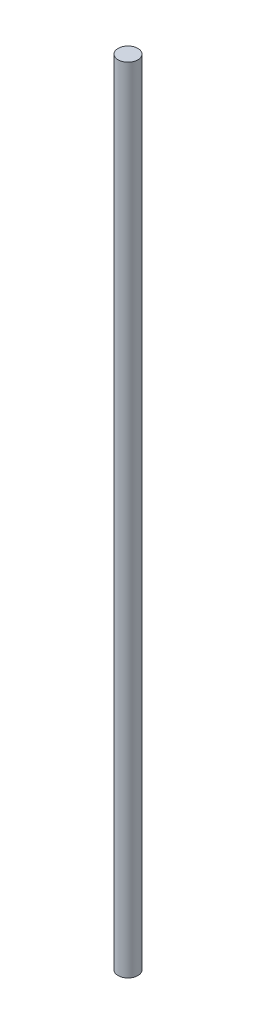
SolidWorks part; units mm, degrees
ref_plane "前视基准面" through (0, 0, 0) normal (0, 0, 1) x (1, 0, 0)
ref_plane "上视基准面" through (0, 0, 0) normal (0, 1, 0) x (1, 0, 0)
ref_plane "右视基准面" through (0, 0, 0) normal (1, 0, 0) x (0, 0, -1)
sketch "草图1" plane through (0, 0, 0) normal (0, 1, 0) x (1, 0, 0)
  circle A0 centre (0, 0) radius 5
extrude "凸台-拉伸2" add sketch "草图1" along normal blind 400 contours A0
